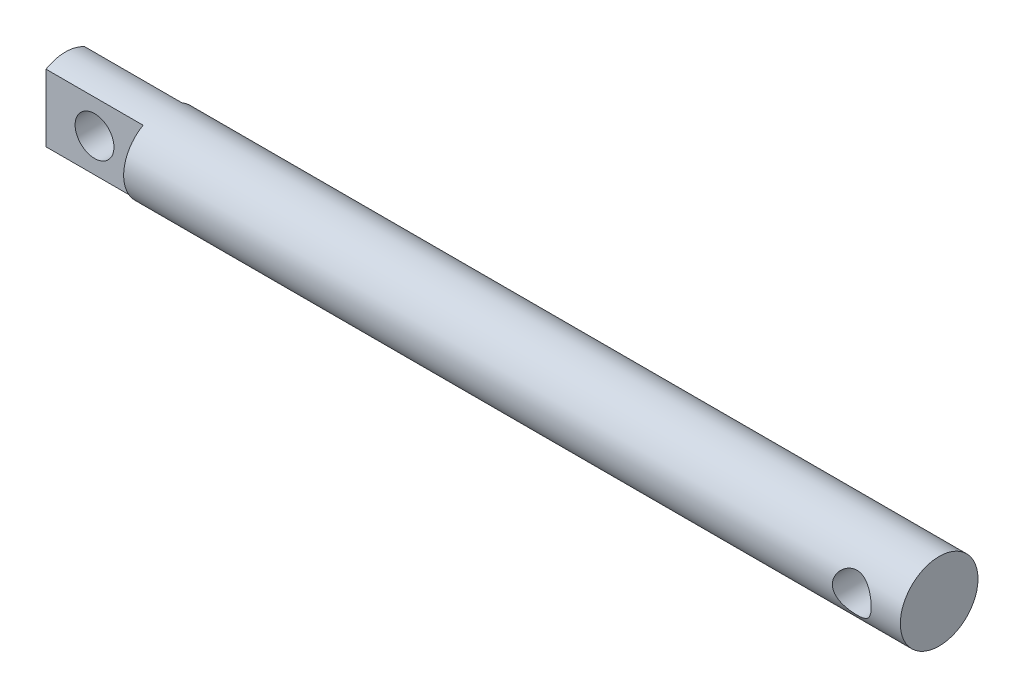
SolidWorks part; units mm, degrees
material "普通碳钢"
ref_plane "前视基准面" through (0, 0, 0) normal (0, 0, 1) x (1, 0, 0)
ref_plane "上视基准面" through (0, 0, 0) normal (0, 1, 0) x (1, 0, 0)
ref_plane "右视基准面" through (0, 0, 0) normal (1, 0, 0) x (0, 0, -1)
sketch "草图1" plane through (0, 0, 0) normal (1, 0, 0) x (0, 0, -1)
  circle A0 centre (0, 0) radius 8
  dimension "D1" = 16
extrude "凸台-拉伸1" add sketch "草图1" along normal blind 180 contours A0
sketch "草图2" plane through (0, 0, 0) normal (0, 0, 1) x (1, 0, 0)
  line L0 (0, 8) -> (0, -8) construction
  line L1 (180, -8) -> (180, 8) construction
  line L2 (0, 0) -> (22.073, 0) construction
  line L3 (170, 0) -> (180, 0) construction
  circle A0 centre (10, 0) radius 4
  circle A1 centre (170, 0) radius 4
  dimension "D1" = 8
  dimension "D2" = 8
  dimension "D3" = 10
  dimension "D4" = 10
extrude "切除-拉伸1" cut sketch "草图2" against normal through all and the other way through all
sketch "草图3" plane through (0, 0, 0) normal (-1, 0, 0) x (0, 0, 1)
  line L0 (-4, 10) -> (-4, -10)
  line L1 (-4, 10) -> (4, 10)
  line L2 (4, 10) -> (4, -10)
  line L3 (-4, -10) -> (4, -10)
  dimension "D1" = 4
  dimension "D2" = 4
  dimension "D3" = 20
  dimension "D4" = 10
extrude "切除-拉伸2" cut sketch "草图3" against normal blind 20 flip side to cut
